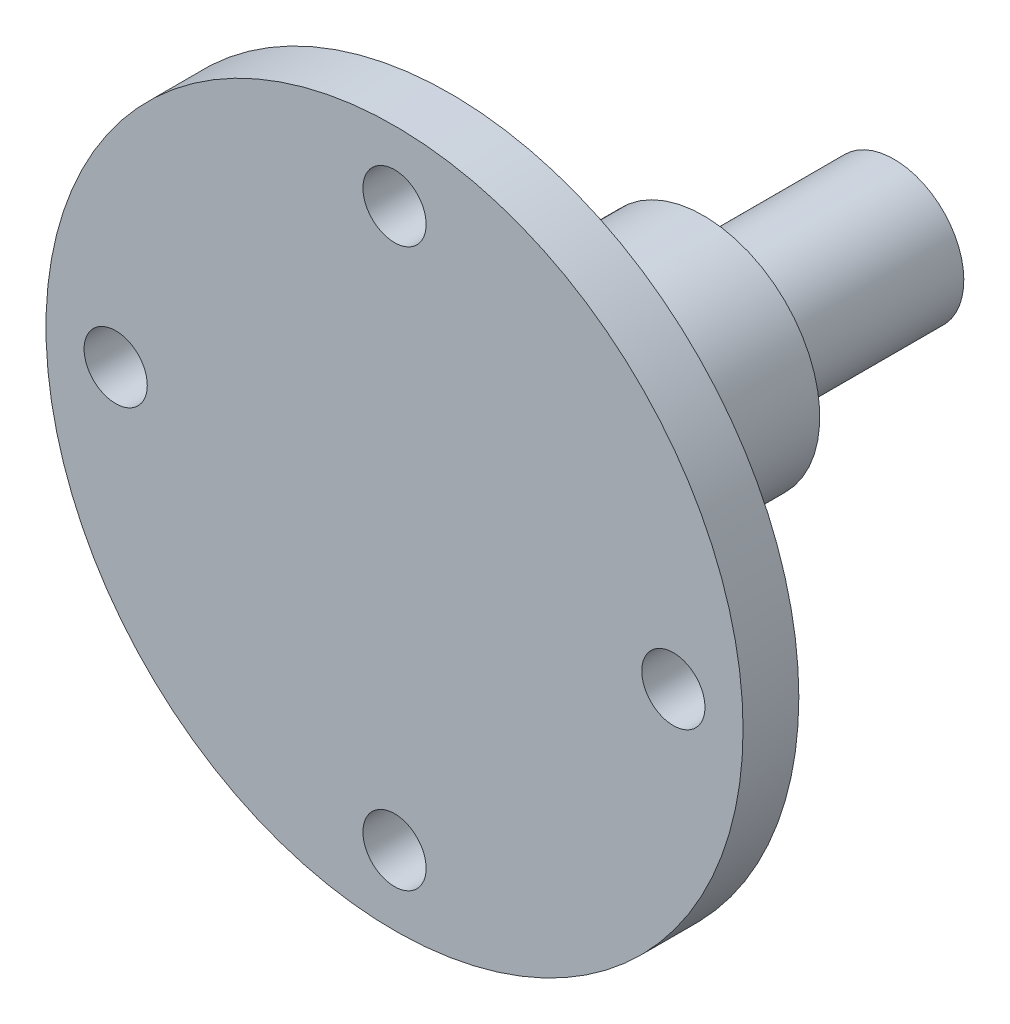
SolidWorks part; units mm, degrees
material "Alumina"
ref_plane "Plan de face" through (0, 0, 0) normal (0, 0, 1) x (1, 0, 0)
ref_plane "Plan de dessus" through (0, 0, 0) normal (0, 1, 0) x (1, 0, 0)
ref_plane "Plan de droite" through (0, 0, 0) normal (1, 0, 0) x (0, 0, -1)
sketch "Sketch1" plane through (0, 0, 0) normal (0, 0, 1) x (1, 0, 0)
  circle A0 centre (0, 0) radius 37.5
  circle A1 centre (0, 0) radius 30 construction
  dimension "D1" = 75
  dimension "D2" = 60
extrude "Boss-Extrude1" add sketch "Sketch1" along normal blind 6
hole_wizard "Trou pour taraudage pour trou taraudé M81" positions "Sketch7" profile "Sketch8" hole size "M8" standard "ISO"
sketch "Sketch7" plane through (0, 0, 6) normal (0, 0, 1) x (1, 0, 0)
  circle A0 centre (0, 0) radius 30 construction
  point P5 (0, 30)
  point P7 (30, 0)
  point P9 (0, -30)
  point P11 (-30, 0)
  dimension "D1" = 60
sketch "Sketch8" plane through (-30, 0, 6) normal (1, 0, 0) x (0, -1, 0)
  line L0 (0, 0) -> (0, 25.0429)
  line L1 (0, 25.0429) -> (3.4, 23)
  line L2 (3.4, 23) -> (3.4, 0)
  line L5 (3.4, 0) -> (0, 0)
  line L10 (0, 25.0429) -> (-3.4, 23) construction
  line L11 (0, -6.35) -> (0, 107.95) construction
  dimension "Hole Dia." = 6.8
  dimension "Hole Depth" = 23
  dimension "Drill Angle" = 118
sketch "Sketch6" plane through (0, 0, 0) normal (0, 0, -1) x (-1, 0, 0)
  circle A0 centre (0, 0) radius 14.5
  dimension "D1" = 29
extrude "Boss.-Extru.1" add sketch "Sketch6" along normal blind 6
sketch "Sketch5" plane through (0, 0, -6) normal (0, 0, -1) x (-1, 0, 0)
  circle A0 centre (0, 0) radius 12.5
  dimension "D1" = 25
extrude "Boss.-Extru.2" add sketch "Sketch5" along normal blind 21.25
sketch "Esquisse11" plane through (0, 0, -27.25) normal (0, 0, -1) x (-1, 0, 0)
  circle A0 centre (0, 0) radius 7.5
  dimension "D1" = 15
extrude "Boss.-Extru.6" add sketch "Esquisse11" along normal blind 20.5
hole_wizard "Trou pour taraudage pour trou taraudé M61" positions "Esquisse9" profile "Esquisse10" hole size "M6" standard "ISO"
sketch "Esquisse9" plane through (0, 0, -47.75) normal (0, 0, -1) x (-1, 0, 0)
  point P0 (0, 0)
sketch "Esquisse10" plane through (0, 0, -47.75) normal (1, 0, 0) x (0, 1, 0)
  line L0 (0, 0) -> (0, 25.5022)
  line L1 (0, 25.5022) -> (2.5, 24)
  line L2 (2.5, 24) -> (2.5, 0)
  line L5 (2.5, 0) -> (0, 0)
  line L10 (0, 25.5022) -> (-2.5, 24) construction
  line L11 (0, -6.35) -> (0, 107.95) construction
  dimension "Diamètre du perçage" = 5
  dimension "Profondeur du perçage" = 24
  dimension "Angle de pointe" = 118
ref_plane "Plan1" through (0, -4.5, 0) normal (0, 1, 0) x (1, 0, 0)
sketch "Esquisse5" plane through (0, -4.5, 0) normal (0, 1, 0) x (1, 0, 0)
  line L0 (0, 47.75) -> (0, 30.75) construction
  line L5 (7.5, 47.75) -> (-7.5, 47.75) construction
  line L6 (2.5, 47.75) -> (2.5, 30.75)
  line L7 (-2.5, 47.75) -> (-2.5, 30.75)
  arc A2 (2.5, 47.75) -> (-2.5, 47.75) centre (0, 47.75) ccw
  arc A3 (-2.5, 30.75) -> (2.5, 30.75) centre (0, 30.75) ccw
  point P4 (0, 39.25)
  dimension "D1" = 5
  dimension "D2" = 17
extrude "Enlèv. mat.-Extru.1" cut sketch "Esquisse5" against normal through all
